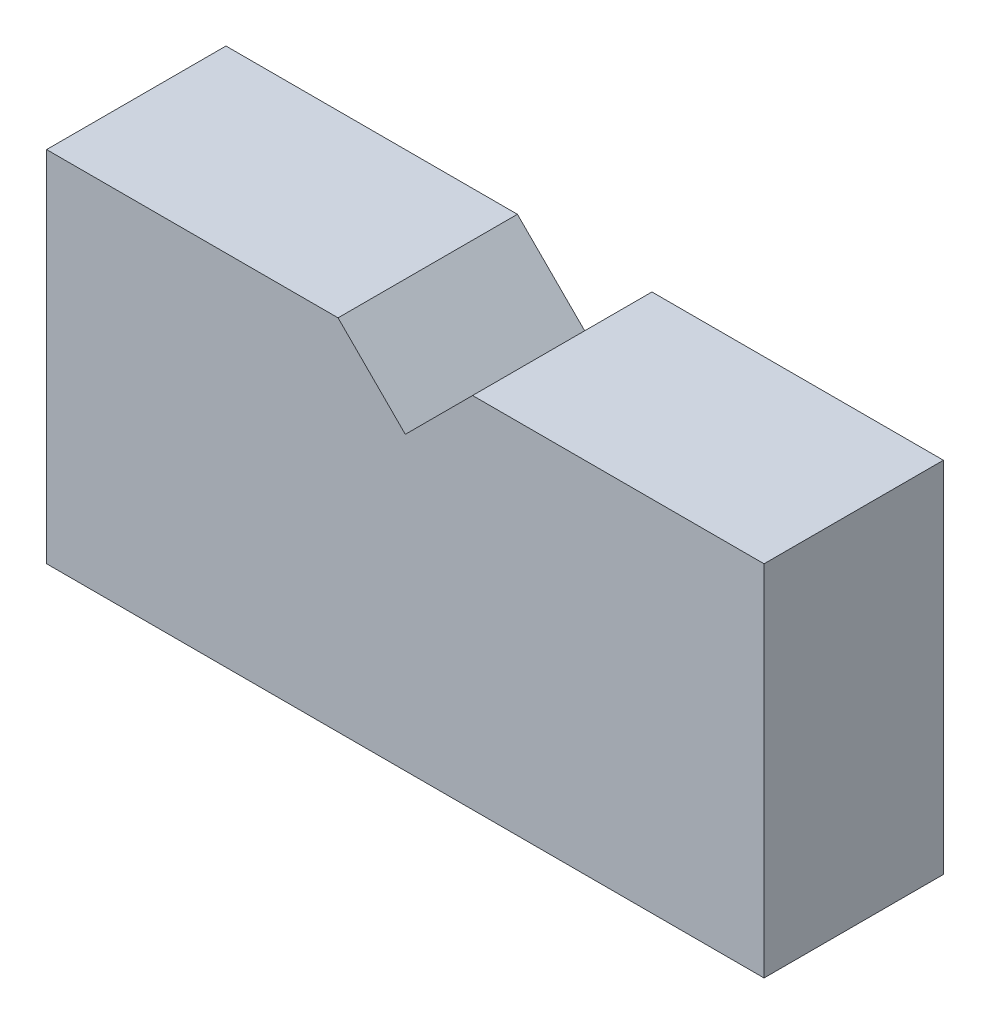
SolidWorks part; units mm, degrees
ref_plane "Front Plane" through (0, 0, 0) normal (0, 0, 1) x (1, 0, 0)
ref_plane "Top Plane" through (0, 0, 0) normal (0, 1, 0) x (1, 0, 0)
ref_plane "Right Plane" through (0, 0, 0) normal (1, 0, 0) x (0, 0, -1)
sketch "Sketch3" plane through (0, 0, 0) normal (0, 0, 1) x (1, 0, 0)
  line L0 (82.55, 101.6) -> (101.6, 82.55)
  line L1 (0, 0) -> (203.2, 0)
  line L2 (0, 0) -> (0, 101.6)
  line L3 (0, 101.6) -> (82.55, 101.6)
  line L4 (203.2, 0) -> (203.2, 101.6)
  line L5 (101.6, 82.55) -> (120.65, 101.6)
  line L6 (120.65, 101.6) -> (203.2, 101.6)
  point P7 (0, 0)
  point P9 (0, 0)
  point P10 (0, 0)
  point P11 (101.6, 0)
  dimension "D1" = 101.6
  dimension "D2" = 203.2
  dimension "D3" = 19.05
  dimension "D4" = 38.1
extrude "Boss-Extrude2" add sketch "Sketch3" along normal mid plane 50.8
